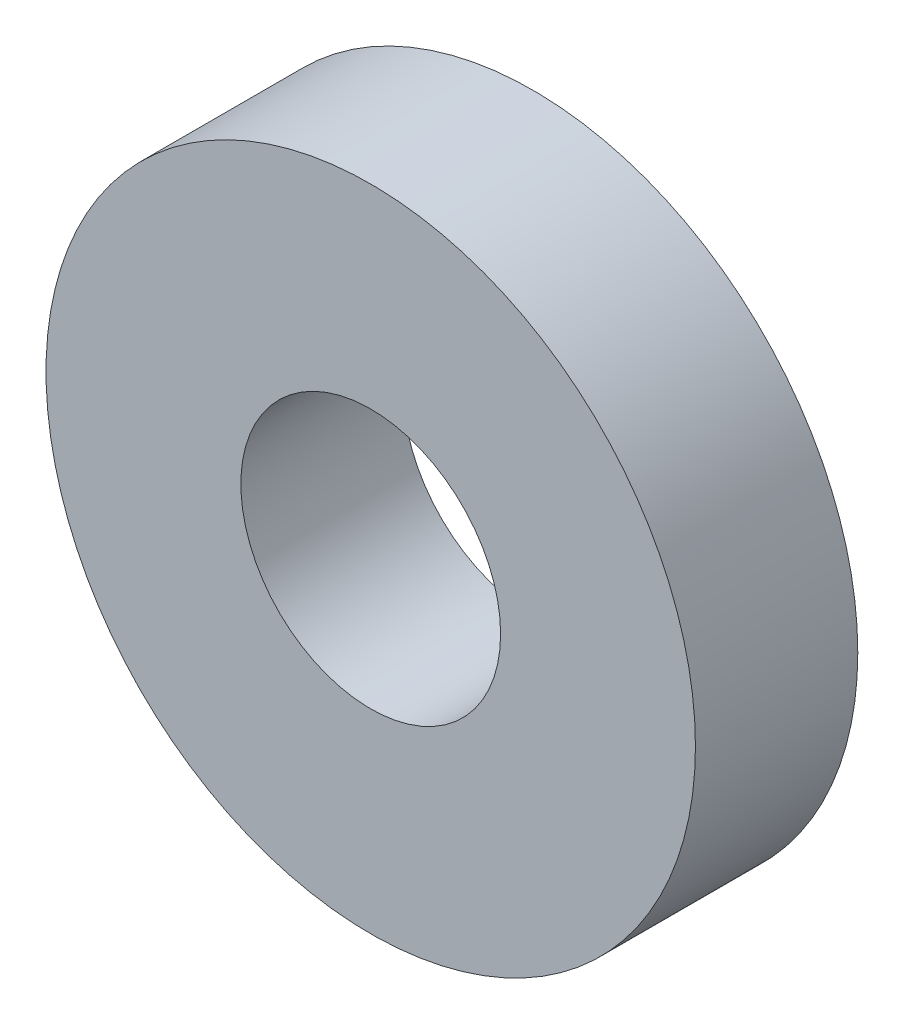
SolidWorks part; units mm, degrees
material "Thornel Mat VMA"
ref_plane "前视基准面" through (0, 0, 0) normal (0, 0, 1) x (1, 0, 0)
ref_plane "上视基准面" through (0, 0, 0) normal (0, 1, 0) x (1, 0, 0)
ref_plane "右视基准面" through (0, 0, 0) normal (1, 0, 0) x (0, 0, -1)
sketch "草图1" plane through (0, 0, 0) normal (0, 0, 1) x (1, 0, 0)
  circle A0 centre (0, 0) radius 10
  circle A1 centre (0, 0) radius 4
  dimension "D1" = 20
  dimension "D2" = 8
extrude "凸台-拉伸1" add sketch "草图1" along normal blind 5 contours A1 | A0
